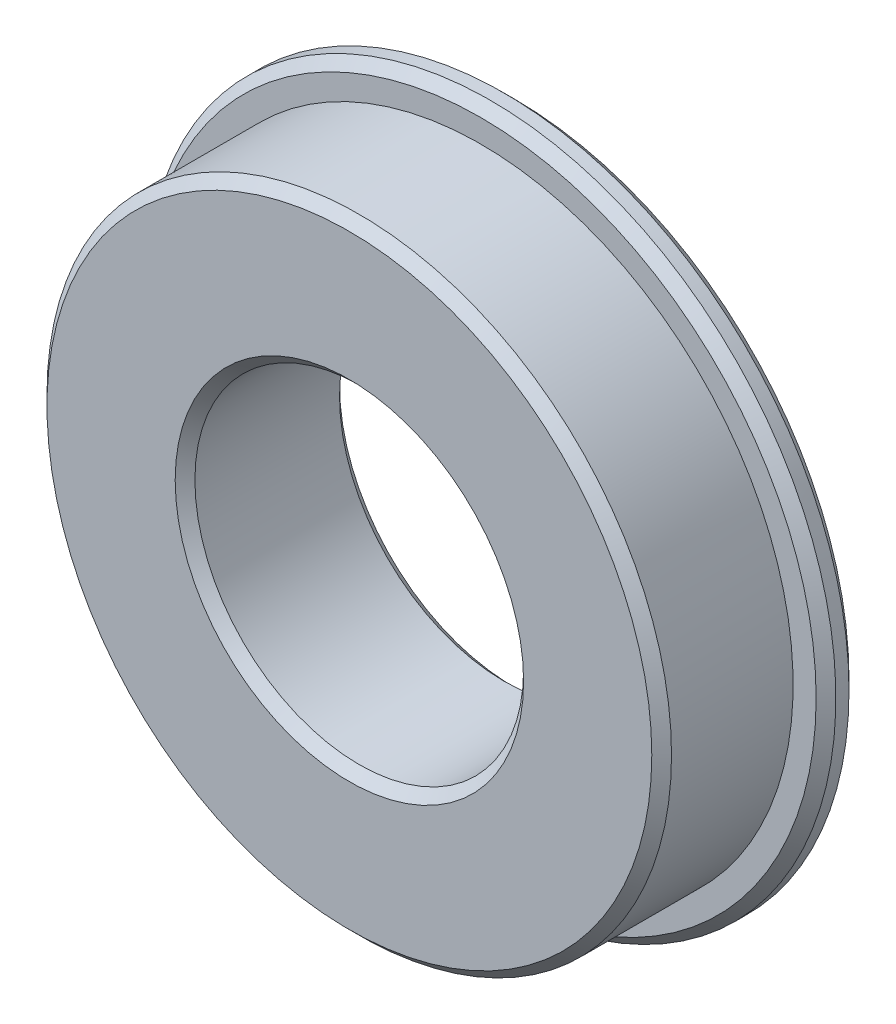
SolidWorks part; units mm, degrees
ref_plane "前视基准面" through (0, 0, 0) normal (0, 0, 1) x (1, 0, 0)
ref_plane "上视基准面" through (0, 0, 0) normal (0, 1, 0) x (1, 0, 0)
ref_plane "右视基准面" through (0, 0, 0) normal (1, 0, 0) x (0, 0, -1)
sketch "草图1" plane through (0, 0, 0) normal (0, 0, 1) x (1, 0, 0)
  circle A0 centre (0, 0) radius 5
  circle A1 centre (0, 0) radius 9.5
  dimension "D1" = 10
  dimension "D2" = 19
extrude "凸台-拉伸1" add sketch "草图1" along normal blind 5
sketch "草图2" plane through (0, 0, 0) normal (0, 0, -1) x (-1, 0, 0)
  circle A0 centre (0, 0) radius 10.5
  circle A1 centre (0, 0) radius 9.5 construction
  circle A2 centre (0, 0) radius 9.5
  dimension "D1" = 21
extrude "凸台-拉伸2" add sketch "草图2" against normal blind 1
chamfer "倒角1" distance 0.3 angle 45 5 edges at (5, 0, 5) (5, 0, 0) (-10.5, 0, 1) (-10.5, 0, 0) (9.5, 0, 5)
